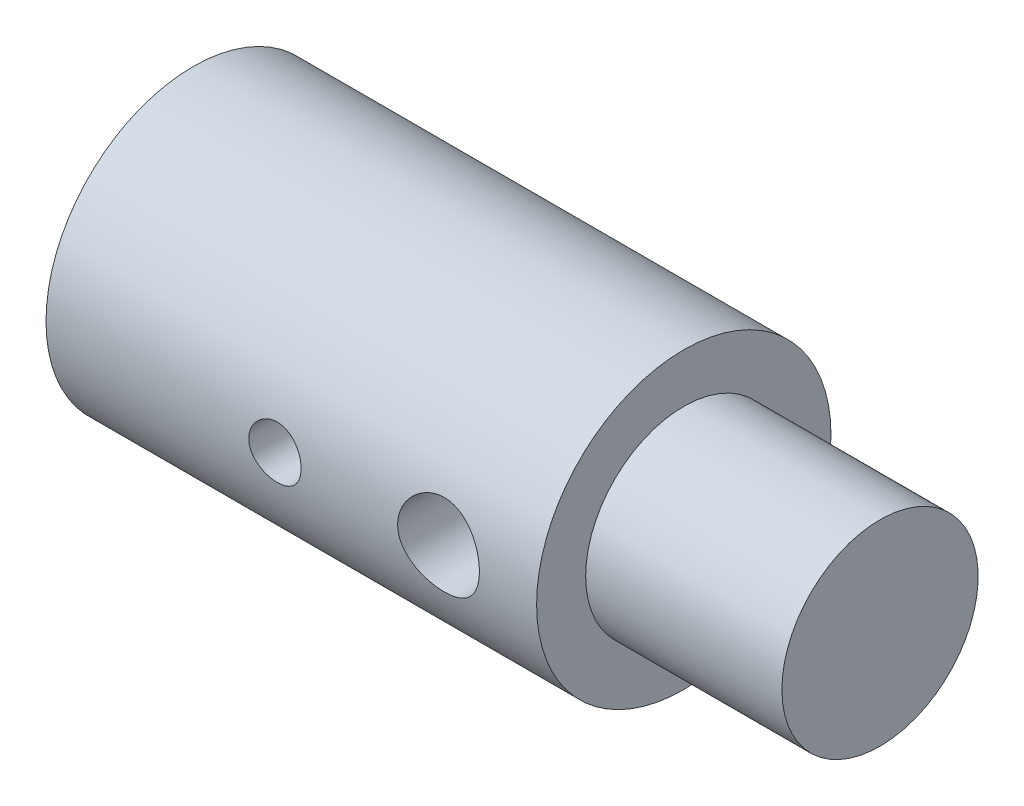
SolidWorks part; units mm, degrees
material "3.0205 (EN-AW 1200)"
ref_plane "Vorne" through (0, 0, 0) normal (0, 0, 1) x (1, 0, 0)
ref_plane "Oben" through (0, 0, 0) normal (0, 1, 0) x (1, 0, 0)
ref_plane "Rechts" through (0, 0, 0) normal (1, 0, 0) x (0, 0, -1)
sketch "Skizze1" plane through (0, 0, 0) normal (0, 0, 1) x (1, 0, 0)
  line L0 (0, 0) -> (71.7919, 0) construction
  line L1 (0, 4.5) -> (0, 2)
  line L2 (0, 2) -> (14, 2)
  line L3 (14, 2) -> (15.2017, 0)
  line L4 (15.2017, 0) -> (21, 0)
  line L5 (21, 0) -> (21, 3)
  line L6 (21, 3) -> (15, 3)
  line L7 (15, 3) -> (15, 4.5)
  line L8 (15, 4.5) -> (0, 4.5)
  dimension "D1" = 4
  dimension "D2" = 6
  dimension "D3" = 6
  dimension "D4" = 59
  dimension "D5" = 14
  dimension "D6" = 9
  dimension "D7" = 15
revolve "Rotation1" add sketch "Skizze1" angle 360 about L0
ref_plane "Ebene1" through (0, 0, -4.5) normal (0, 0, -1) x (-1, 0, 0)
hole_wizard "M2 Gewindebohrung1" positions "Skizze6" profile "Skizze5" tap size "M2" standard "Iso"
sketch "Skizze6" plane through (0, 0, 0) normal (0, 0, 1) x (1, 0, 0)
  point P0 (7, 0)
  dimension "D1" = 7
sketch "Skizze5" plane through (7, 0, 0) normal (1, 0, 0) x (0, 1, 0)
  line L0 (0, 0) -> (0, 4.5)
  line L1 (0, 4.5) -> (0.8, 4.5)
  line L2 (0.8, 4.5) -> (0.8, 0)
  line L5 (0.8, 0) -> (0, 0)
  line L11 (0, -6.35) -> (0, 107.95) construction
  dimension "Nenndurchmesser (Haupt)" = 1.6
  dimension "Bohrungstiefe" = 4.5
cosmetic thread "Gewindedarstellung1"
sketch "Skizze7" plane through (0, 0, 0) normal (0, 0, 1) x (1, 0, 0)
  circle A0 centre (12, 0) radius 1.25
  dimension "D1" = 2.5
  dimension "D2" = 12
extrude "Schnitt-Linear austragen2" cut sketch "Skizze7" against normal through all and the other way through all
move or copy body "Körper-Verschieben/Kopieren1" [suppressed] bodies to move or copy 107
